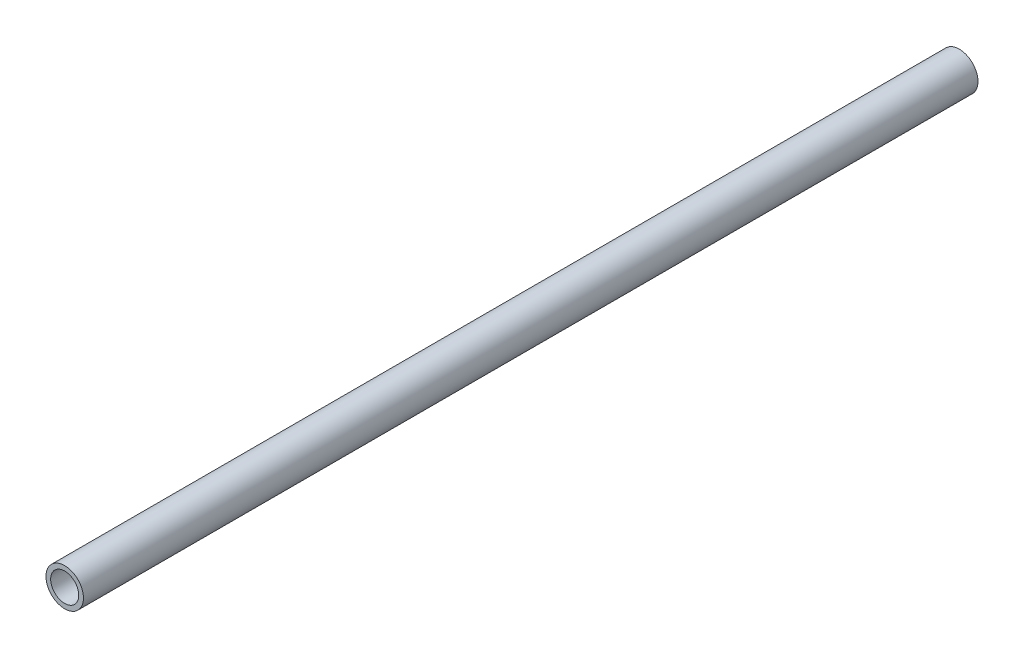
SolidWorks part; units mm, degrees
ref_plane "前视基准面" through (0, 0, 0) normal (0, 0, 1) x (1, 0, 0)
ref_plane "上视基准面" through (0, 0, 0) normal (0, 1, 0) x (1, 0, 0)
ref_plane "右视基准面" through (0, 0, 0) normal (1, 0, 0) x (0, 0, -1)
sketch "草图1" plane through (0, 0, 0) normal (0, 0, 1) x (1, 0, 0)
  circle A0 centre (0, 0) radius 6
  circle A1 centre (0, 0) radius 8
  dimension "D1" = 12
  dimension "D2" = 16
extrude "凸台-拉伸1" add sketch "草图1" along normal blind 382
